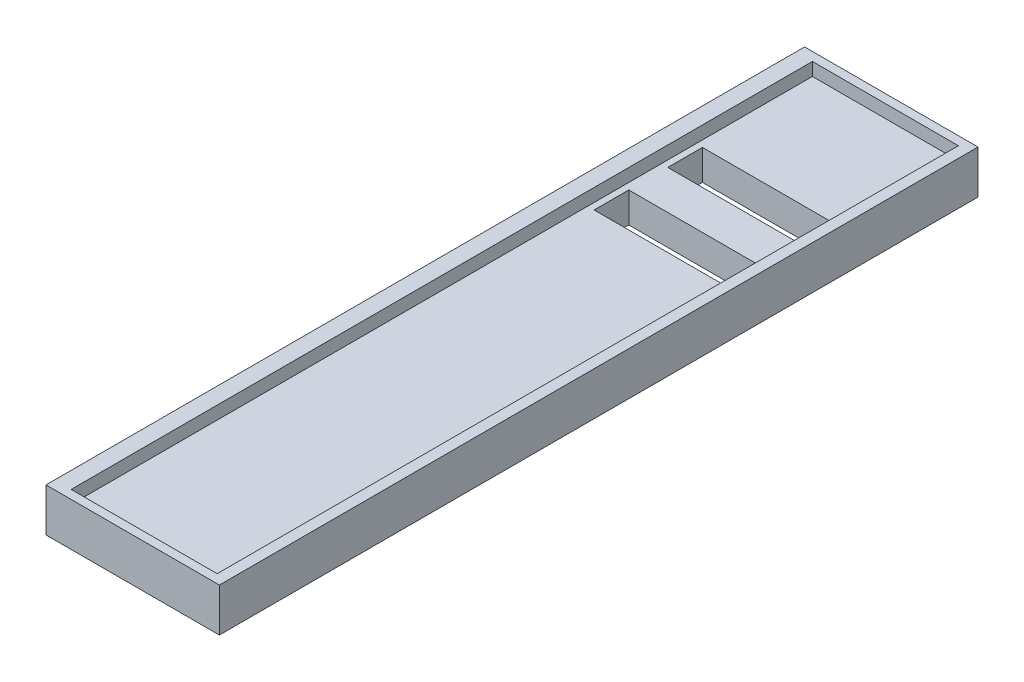
SolidWorks part; units mm, degrees
ref_plane "前视基准面" through (0, 0, 0) normal (0, 0, 1) x (1, 0, 0)
ref_plane "上视基准面" through (0, 0, 0) normal (0, 1, 0) x (1, 0, 0)
ref_plane "右视基准面" through (0, 0, 0) normal (1, 0, 0) x (0, 0, -1)
sketch "草图1" plane through (0, 0, 0) normal (0, 0, 1) x (1, 0, 0)
  line L1 (-45.8316, 4.4148) -> (34.1684, 4.4148)
  line L2 (-45.8316, 4.4148) -> (-45.8316, -15.5852)
  line L3 (-45.8316, -15.5852) -> (34.1684, -15.5852)
  line L4 (34.1684, 4.4148) -> (34.1684, -15.5852)
  dimension "D1" = 80
  dimension "D2" = 20
extrude "凸台-拉伸1" add sketch "草图1" along normal blind 350
sketch "草图2" plane through (0, 0, 350) normal (0, 0, 1) x (1, 0, 0)
  line L0 (34.1684, 4.4148) -> (-45.8316, 4.4148) construction
  line L1 (-38.2318, 4.4148) -> (29.1238, 4.4148)
  line L2 (-38.2318, 4.4148) -> (-38.2318, -1.5852)
  line L3 (-38.2318, -1.5852) -> (29.1238, -1.5852)
  line L4 (29.1238, 4.4148) -> (29.1238, -1.5852)
  dimension "D1" = 6
extrude "切除-拉伸1" cut sketch "草图2" against normal through all
sketch "草图3" plane through (0, -1.5852, 0) normal (0, 1, 0) x (1, 0, 0)
  line L1 (-35.2505, -73.7113) -> (25.0515, -73.7113)
  line L2 (-35.2505, -73.7113) -> (-35.2505, -57.7113)
  line L3 (-35.2505, -57.7113) -> (25.0515, -57.7113)
  line L4 (25.0515, -73.7113) -> (25.0515, -57.7113)
  line L5 (-35.2505, -91.7113) -> (25.0515, -91.7113)
  line L6 (-35.2505, -91.7113) -> (-35.2505, -107.7113)
  line L7 (-35.2505, -107.7113) -> (25.0515, -107.7113)
  line L8 (25.0515, -91.7113) -> (25.0515, -107.7113)
  dimension "D1" = 18
  dimension "D2" = 16
  dimension "D3" = 16
extrude "切除-拉伸2" cut sketch "草图3" against normal through all
sketch "草图4" plane through (0, 0, 350) normal (0, 0, 1) x (1, 0, 0)
  line L1 (-38.2318, 4.4148) -> (29.1238, 4.4148)
  line L2 (-38.2318, 4.4148) -> (-38.2318, -1.5852)
  line L3 (-38.2318, -1.5852) -> (29.1238, -1.5852)
  line L4 (29.1238, 4.4148) -> (29.1238, -1.5852)
extrude "凸台-拉伸2" add sketch "草图4" against normal blind 4
sketch "草图5" plane through (0, 0, 0) normal (0, 0, -1) x (-1, 0, 0)
  line L0 (-29.1238, -1.5852) -> (-29.1238, 4.4148) construction
  line L1 (-29.1238, 4.4148) -> (38.2318, 4.4148)
  line L2 (-29.1238, 4.4148) -> (-29.1238, -1.5852)
  line L3 (-29.1238, -1.5852) -> (38.2318, -1.5852)
  line L4 (38.2318, 4.4148) -> (38.2318, -1.5852)
  line L5 (-34.1684, 4.4148) -> (-29.1238, 4.4148) construction
extrude "凸台-拉伸3" add sketch "草图5" against normal blind 4
